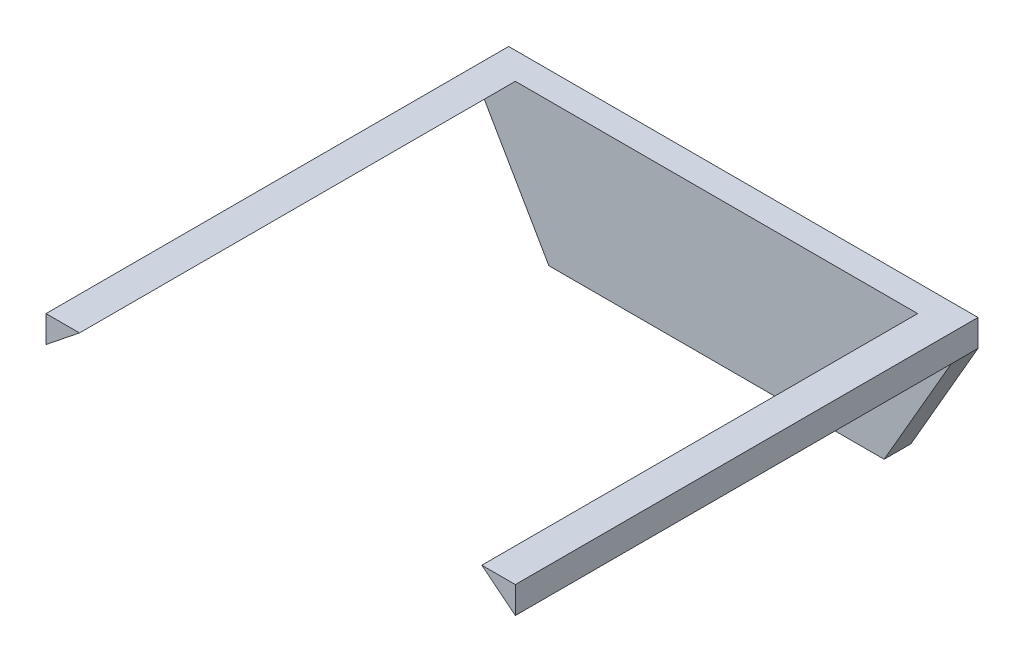
SolidWorks part; units mm, degrees
ref_plane "Front Plane" through (0, 0, 0) normal (0, 0, 1) x (1, 0, 0)
ref_plane "Top Plane" through (0, 0, 0) normal (0, 1, 0) x (1, 0, 0)
ref_plane "Right Plane" through (0, 0, 0) normal (1, 0, 0) x (0, 0, -1)
sketch "Sketch1" plane through (0, 0, 0) normal (0, 0, 1) x (1, 0, 0)
  line L0 (0, 0) -> (-63.5, 0)
  line L1 (-63.5, 0) -> (-76.2, 21.997)
  line L2 (0, 0) -> (12.7, 21.997)
  line L3 (-76.2, 21.997) -> (-76.2, 27.077)
  line L4 (12.7, 21.997) -> (12.7, 27.077)
  line L5 (-76.2, 27.077) -> (12.7, 27.077)
  dimension "D1" = 120
  dimension "D2" = 120
  dimension "D3" = 63.5
  dimension "D4" = 25.4
  dimension "D5" = 25.4
  dimension "D6" = 5.08
  dimension "D7" = 5.08
extrude "Boss-Extrude1" add sketch "Sketch1" along normal blind 5.08
sketch "Sketch2" plane through (0, 0, 5.08) normal (0, 0, 1) x (1, 0, 0)
  line L0 (-76.2, 21.997) -> (-69.85, 27.077)
  line L1 (12.7, 27.077) -> (-76.2, 27.077) construction
  line L2 (-76.2, 21.997) -> (-76.2, 27.077)
  line L3 (-76.2, 27.077) -> (-69.85, 27.077)
  line L4 (12.7, 21.997) -> (12.7, 27.077)
  line L5 (12.7, 27.077) -> (6.35, 27.077)
  line L6 (6.35, 27.077) -> (12.7, 21.997)
  point P5 (-69.85, 27.077)
  point P13 (6.35, 27.077)
  dimension "D1" = 6.35
  dimension "D3" = 6.35
extrude "Boss-Extrude2" add sketch "Sketch2" along normal blind 82.55
